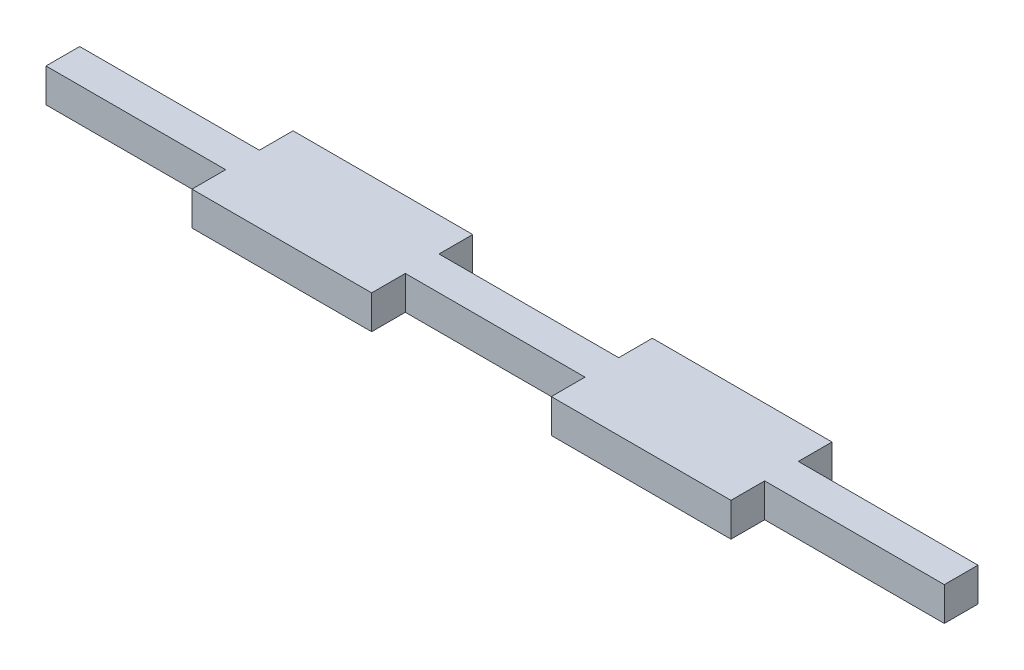
SolidWorks part; units mm, degrees
ref_plane "Ön Düzlem" through (0, 0, 0) normal (0, 0, 1) x (1, 0, 0)
ref_plane "Üst Düzlem" through (0, 0, 0) normal (0, 1, 0) x (1, 0, 0)
ref_plane "Sağ Düzlem" through (0, 0, 0) normal (1, 0, 0) x (0, 0, -1)
sketch "Sketch1" plane through (0, 0, 0) normal (0, 1, 0) x (1, 0, 0)
  line L1 (-24, -4.5) -> (-8, -4.5)
  line L2 (-40, -1.5) -> (-40, 1.5)
  line L3 (-24, 4.5) -> (-8, 4.5)
  line L4 (40, -1.5) -> (40, 1.5)
  line L5 (-24, -2.7) -> (40, 4.5) construction
  line L6 (-40, 4.5) -> (24, -2.7) construction
  line L7 (-40, 1.5) -> (-24, 1.5)
  line L8 (-24, 1.5) -> (-24, 4.5)
  line L9 (-24, -4.5) -> (-24, -1.5)
  line L10 (-8, 4.5) -> (-8, 1.5)
  line L11 (-8, 1.5) -> (8, 1.5)
  line L12 (8, 1.5) -> (8, 4.5)
  line L13 (8, 4.5) -> (24, 4.5)
  line L14 (24, 4.5) -> (24, 1.5)
  line L15 (24, 1.5) -> (40, 1.5)
  line L16 (-24, -1.5) -> (-40, -1.5)
  line L17 (-8, -4.5) -> (-8, -1.5)
  line L18 (-8, -1.5) -> (8, -1.5)
  line L19 (8, -1.5) -> (8, -4.5)
  line L20 (8, -4.5) -> (24, -4.5)
  line L21 (24, -4.5) -> (24, -1.5)
  line L22 (24, -1.5) -> (40, -1.5)
  point P0 (0, 0)
  dimension "D1" = 80
extrude "Boss-Extrude2" add sketch "Sketch1" along normal blind 3
